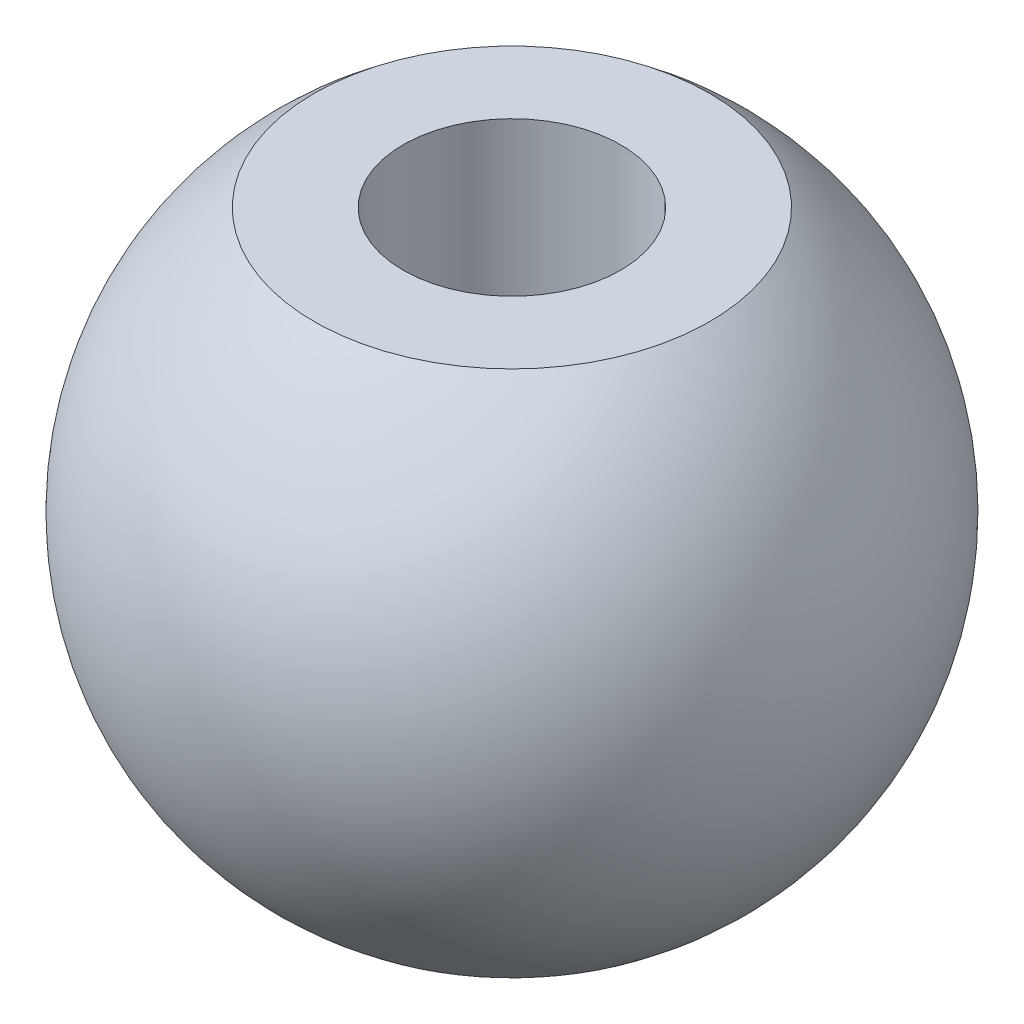
SolidWorks part; units mm, degrees
ref_plane "Front Plane" through (0, 0, 0) normal (0, 0, 1) x (1, 0, 0)
ref_plane "Top Plane" through (0, 0, 0) normal (0, 1, 0) x (1, 0, 0)
ref_plane "Right Plane" through (0, 0, 0) normal (1, 0, 0) x (0, 0, -1)
sketch "Sketch1" plane through (0, 0, 0) normal (0, 0, 1) x (1, 0, 0)
  line L0 (0, 0) -> (0, 10) construction
  line L1 (0, 9) -> (3, 9)
  line L2 (0, 0) -> (0, 9)
  arc A0 (0, 10) -> (0, 0) centre (0, 5) cw construction
  arc A1 (3, 9) -> (0, 0) centre (0, 5) cw
  dimension "D1" = 10
  dimension "D2" = 1
revolve "Revolve1" add sketch "Sketch1" angle 360 about L0
hole_wizard "Tap Drill for M4x0.7 Tap1" positions "Sketch2" profile "Sketch3" hole size "M4x0.7" standard "ANSI Metric"
sketch "Sketch2" plane through (0, 9, 0) normal (0, 1, 0) x (1, 0, 0)
  point P0 (0, 0)
  point P3 (-17.9908, 5.7505)
sketch "Sketch3" plane through (0, 9, 0) normal (1, 0, 0) x (0, 0, 1)
  line L0 (0, 0) -> (0, 6.9914)
  line L1 (0, 6.9914) -> (1.65, 6)
  line L2 (1.65, 6) -> (1.65, 0)
  line L5 (1.65, 0) -> (0, 0)
  line L10 (0, 6.9914) -> (-1.65, 6) construction
  line L11 (0, -6.35) -> (0, 107.95) construction
  dimension "Hole Dia." = 3.3
  dimension "Hole Depth" = 6
  dimension "Drill Angle" = 118
